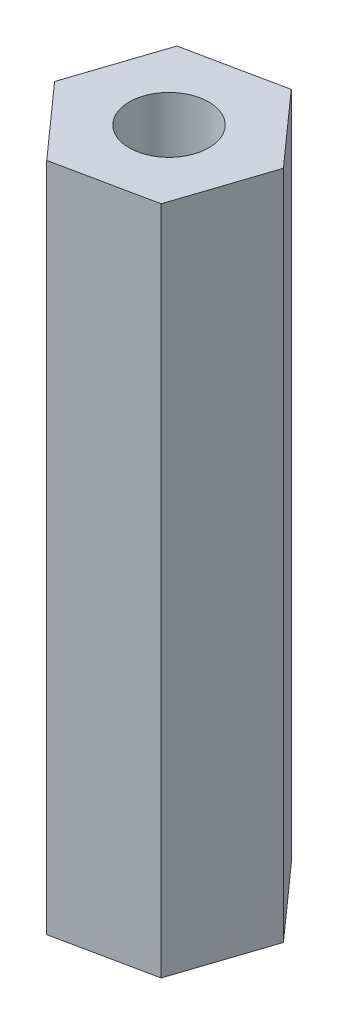
SolidWorks part; units mm, degrees
ref_plane "Front Plane" through (0, 0, 0) normal (0, 0, 1) x (1, 0, 0)
ref_plane "Top Plane" through (0, 0, 0) normal (0, 1, 0) x (1, 0, 0)
ref_plane "Right Plane" through (0, 0, 0) normal (1, 0, 0) x (0, 0, -1)
sketch "Sketch1" plane through (0, 0, 0) normal (0, 1, 0) x (1, 0, 0)
  line L1 (-5.1401, 1.2321) -> (-4.2772, 3.8429)
  line L2 (-4.2772, 3.8429) -> (-6.1067, 5.8955)
  line L3 (-6.1067, 5.8955) -> (-8.7991, 5.3374)
  line L4 (-8.7991, 5.3374) -> (-9.662, 2.7267)
  line L5 (-9.662, 2.7267) -> (-7.8325, 0.674)
  line L6 (-7.8325, 0.674) -> (-5.1401, 1.2321)
  circle A0 centre (-6.9696, 3.2848) radius 2.3813 construction
  circle A1 centre (-6.9696, 3.2848) radius 1.1303
  dimension "D2" = 2.2606
  dimension "D1" = 4.7625
extrude "Boss-Extrude1" add sketch "Sketch1" along normal blind 19.05
